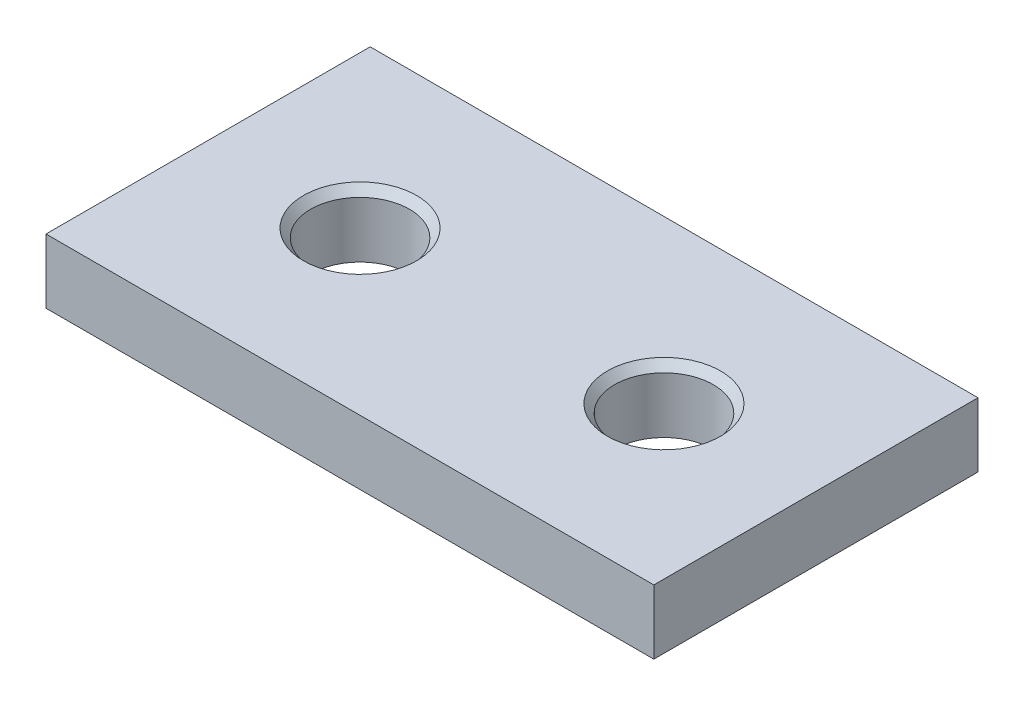
SolidWorks part; units mm, degrees
material "6061-T6 (SS)"
ref_plane "Front Plane" through (0, 0, 0) normal (0, 0, 1) x (1, 0, 0)
ref_plane "Top Plane" through (0, 0, 0) normal (0, 1, 0) x (1, 0, 0)
ref_plane "Right Plane" through (0, 0, 0) normal (1, 0, 0) x (0, 0, -1)
sketch "Sketch1" plane through (0, 0, 0) normal (0, 1, 0) x (1, 0, 0)
  line L1 (-7.5, 4) -> (7.5, 4)
  line L2 (-7.5, 4) -> (-7.5, -4)
  line L3 (-7.5, -4) -> (7.5, -4)
  line L4 (7.5, 4) -> (7.5, -4)
  line L5 (-7.5, 4) -> (7.5, -4) construction
  line L6 (-7.5, -4) -> (7.5, 4) construction
  point P0 (0, 0)
  dimension "D1" = 8
  dimension "D2" = 15
extrude "Boss-Extrude1" add sketch "Sketch1" along normal blind 1.5875
hole_wizard "#2 Clearance Hole1" positions "Sketch3" profile "Sketch2" hole size "#2" standard "ANSI Inch"
sketch "Sketch3" plane through (0, 1.5875, 0) normal (0, 1, 0) x (1, 0, 0)
  line L0 (0, 0) -> (0, -10.1007) construction
  line L1 (0, 0) -> (-7.5, 0) construction
  line L3 (-7.5, 4) -> (-7.5, -4) construction
  point P0 (-3.75, 0)
  point P13 (-3.75, 0)
  point P14 (3.75, 0)
sketch "Sketch2" plane through (-3.75, 1.5875, 0) normal (1, 0, 0) x (0, 0, 1)
  line L0 (0, 0) -> (0, 65.4826)
  line L1 (0, 65.4826) -> (1.2192, 64.75)
  line L2 (1.2192, 64.75) -> (1.2192, 0.2045)
  line L3 (1.2192, 0.2045) -> (1.397, 0)
  line L5 (1.397, 0) -> (0, 0)
  line L6 (-1.2192, 0.2045) -> (-1.397, 0) construction
  line L10 (0, 65.4826) -> (-1.2192, 64.75) construction
  line L11 (0, -6.35) -> (0, 107.95) construction
  dimension "Hole Dia." = 2.4384
  dimension "Hole Depth" = 64.75
  dimension "Near C'Sink Dia." = 2.794
  dimension "Near C'Sink Angle" = 82
  dimension "Drill Angle" = 118
